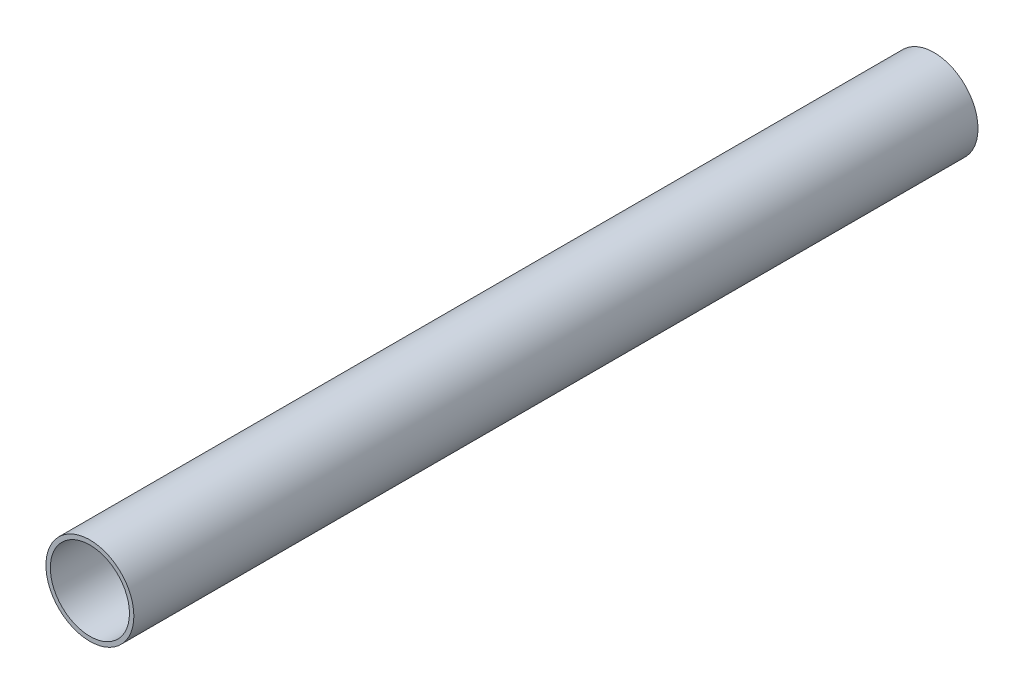
SolidWorks part; units mm, degrees
material "1060 Alloy"
ref_plane "Front Plane" through (0, 0, 0) normal (0, 0, 1) x (1, 0, 0)
ref_plane "Top Plane" through (0, 0, 0) normal (0, 1, 0) x (1, 0, 0)
ref_plane "Right Plane" through (0, 0, 0) normal (1, 0, 0) x (0, 0, -1)
sketch "Sketch1" plane through (0, 0, 0) normal (0, 0, 1) x (1, 0, 0)
  circle A0 centre (0, 0) radius 31.75
  circle A1 centre (0, 0) radius 28.575
  dimension "D1" = 63.5
  dimension "D2" = 57.15
extrude "Boss-Extrude1" add sketch "Sketch1" along normal blind 609.6
